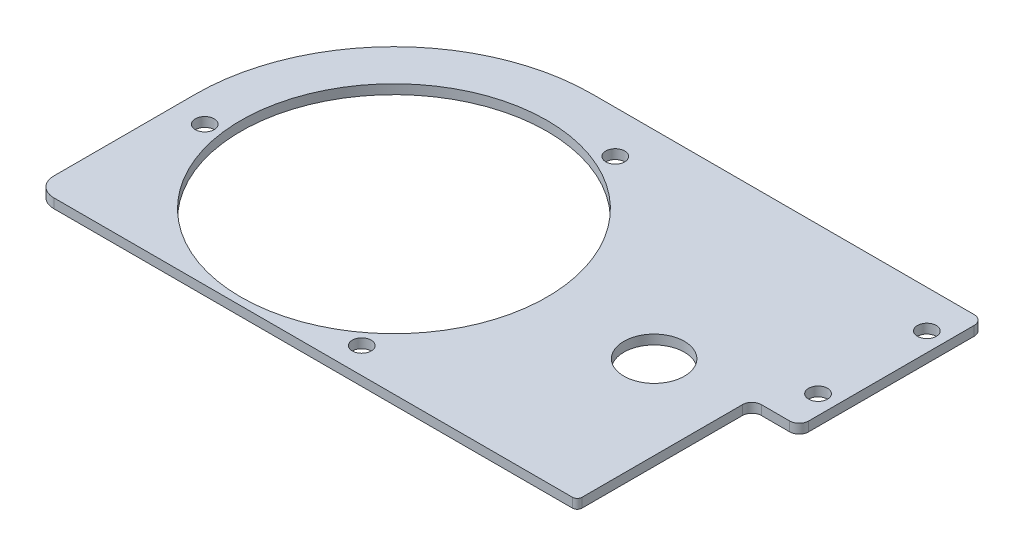
SolidWorks part; units mm, degrees
ref_plane "Front Plane" through (0, 0, 0) normal (0, 0, 1) x (1, 0, 0)
ref_plane "Top Plane" through (0, 0, 0) normal (0, 1, 0) x (1, 0, 0)
ref_plane "Right Plane" through (0, 0, 0) normal (1, 0, 0) x (0, 0, -1)
sketch "Sketch1" plane through (0, 0, 0) normal (0, 1, 0) x (1, 0, 0)
  line L0 (0, 114.3) -> (0, -101.6) construction
  line L1 (256.5211, 133.3689) -> (0, 133.3689)
  line L2 (262.8711, 127.0189) -> (262.8711, 15.8008)
  line L3 (227.9555, -107.9311) -> (-120.6689, -107.9311)
  line L4 (-133.3689, 0) -> (-133.3689, -95.2311)
  line L5 (237.4711, 9.4508) -> (256.5211, 9.4508)
  line L6 (250.1711, 9.4508) -> (250.1711, 133.3689) construction
  line L7 (0, 0) -> (-133.3689, 0) construction
  line L8 (0, 0) -> (-133.3689, -3.0078) construction
  line L11 (231.1211, -104.7655) -> (231.1211, 3.1008)
  circle A0 centre (0, 0) radius 102.87
  circle A1 centre (0, 0) radius 114.3 construction
  circle A2 centre (-112.7386, -14.375) radius 6.35
  arc A3 (237.4711, 9.4508) -> (231.1211, 3.1008) centre (237.4711, 3.1008) ccw
  arc A4 (-133.3689, 0) -> (0, 133.3689) centre (0, 0) cw
  circle A5 centre (43.9202, 104.822) radius 6.35
  circle A6 centre (68.8184, -90.447) radius 6.35
  arc A7 (-120.6689, -107.9311) -> (-133.3689, -95.2311) centre (-120.6689, -95.2311) cw
  arc A8 (227.9555, -107.9311) -> (231.1211, -104.7655) centre (227.9555, -104.7655) ccw
  arc A9 (262.8711, 15.8008) -> (256.5211, 9.4508) centre (256.5211, 15.8008) cw
  arc A10 (256.5211, 133.3689) -> (262.8711, 127.0189) centre (256.5211, 127.0189) cw
  circle A11 centre (250.1711, 107.9689) radius 6.35
  circle A12 centre (250.1711, 34.8508) radius 6.35
  circle A13 centre (-112.7386, -14.375) radius 6.35 construction
  point P0 (0, 0)
  point P11 (0, 0)
  point P12 (246.9961, 9.4508)
  point P32 (231.1211, -107.9311)
  point P46 (0, 0)
  dimension "D3" = 205.74
  dimension "D5" = 228.6
  dimension "D6" = 12.7
  dimension "D7" = 123.9181
  dimension "D8" = 133.3689
  dimension "D11" = 31.75
  dimension "D12" = 25.4
  dimension "D14" = 12.7
  dimension "D9" = 6.35
  dimension "D10" = 12.7
  dimension "D2" = 117.3819
  dimension "D4" = 113.6514
  dimension "D13" = 12.7
  dimension "D15" = 25.4
  dimension "D16" = 396.24
  dimension "D17" = 3
extrude "Boss-Extrude1" add sketch "Sketch1" along normal blind 6.35
sketch "Sketch3" plane through (0, 6.35, 0) normal (0, 1, 0) x (1, 0, 0)
  line L0 (73.0061, 133.3689) -> (73.0061, -107.9311) construction
  line L5 (382.3904, 12.7189) -> (-202.4477, 12.7189) construction
  line L6 (333.3561, -152.3811) -> (-187.3439, -152.3811)
  line L7 (333.3561, -152.3811) -> (333.3561, 177.8189)
  line L8 (333.3561, 177.8189) -> (-187.3439, 177.8189)
  line L9 (-187.3439, -152.3811) -> (-187.3439, 177.8189)
  line L10 (333.3561, -152.3811) -> (-187.3439, 177.8189) construction
  line L11 (333.3561, 177.8189) -> (-187.3439, -152.3811) construction
  line L26 (262.8711, 15.8008) -> (262.8711, 127.0189) construction
  line L27 (-133.3689, 0) -> (-133.3689, -95.2311) construction
  line L28 (-120.6689, -107.9311) -> (227.9555, -107.9311) construction
  line L29 (256.5211, 133.3689) -> (0, 133.3689) construction
  line L30 (262.8711, 15.8008) -> (262.8711, 127.0189)
  line L31 (-133.3689, 0) -> (-133.3689, -95.2311)
  line L32 (-120.6689, -107.9311) -> (227.9555, -107.9311)
  line L33 (256.5211, 133.3689) -> (0, 133.3689)
  point P1 (73.0061, 12.7189)
  dimension "D1" = 520.7
  dimension "D2" = 206.375
  dimension "D3" = 330.2
  dimension "D4" = 120.65
  dimension "D7" = 396.24
  dimension "D8" = 241.3
sketch "Sketch5" plane through (0, 0, 0) normal (0, 1, 0) x (1, 0, 0)
  line L0 (0, 0) -> (199.388, 6.4085) construction
  line L1 (210.8179, 6.3778) -> (187.958, 6.4392) construction
  circle A1 centre (161.8454, 5.2018) radius 11.176 construction
  point P7 (0, 0)
sketch "Sketch6" plane through (0, 0, 0) normal (0, 1, 0) x (1, 0, 0)
  line L0 (6.35, 0) -> (5.207, 0) construction
  line L1 (0, 0) -> (229.1642, 0.1635) construction
  circle A0 centre (174.733, 0.1247) radius 20.32
  circle A1 centre (0, 0) radius 6.35 construction
  circle A2 centre (0, 0) radius 5.207 construction
  point P10 (0, 0)
  dimension "D1" = 40.64
extrude "Cut-Extrude1" cut sketch "Sketch6" along normal blind 28.448
